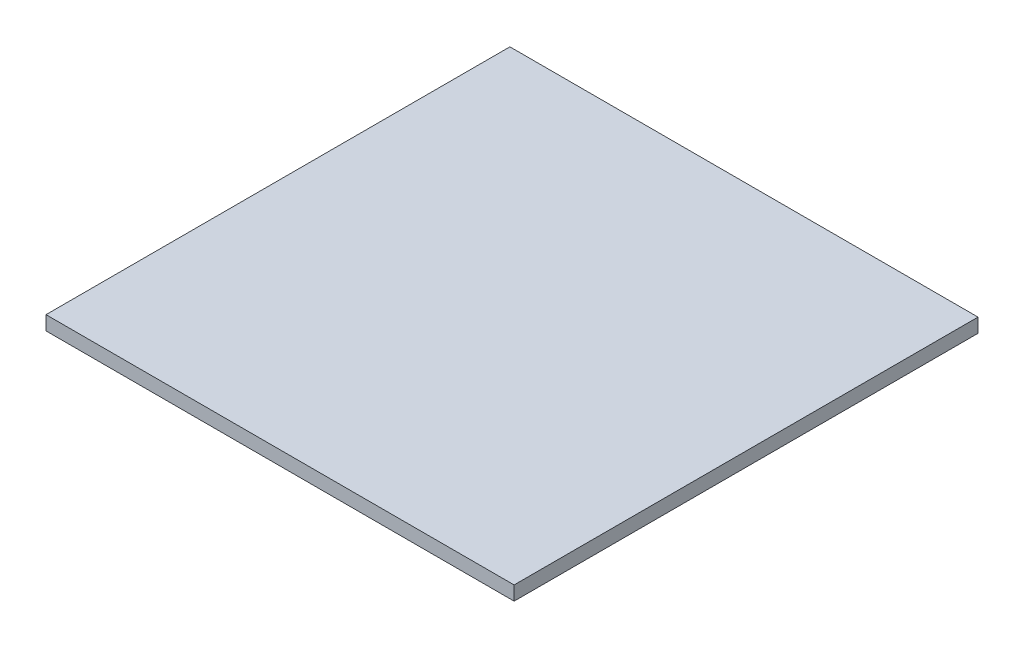
SolidWorks part; units mm, degrees
ref_plane "Front Plane" through (0, 0, 0) normal (0, 0, 1) x (1, 0, 0)
ref_plane "Top Plane" through (0, 0, 0) normal (0, 1, 0) x (1, 0, 0)
ref_plane "Right Plane" through (0, 0, 0) normal (1, 0, 0) x (0, 0, -1)
sketch "Sketch1" plane through (0, 0, 0) normal (0, 1, 0) x (1, 0, 0)
  line L1 (-44.2815, 20.698) -> (55.4185, 20.698)
  line L2 (-44.2815, 20.698) -> (-44.2815, -78.102)
  line L3 (-44.2815, -78.102) -> (55.4185, -78.102)
  line L4 (55.4185, 20.698) -> (55.4185, -78.102)
  dimension "D1" = 99.7
  dimension "D2" = 98.8
extrude "Boss-Extrude1" add sketch "Sketch1" along normal blind 3
equation "\"Fit\"= 1"
equation "\"cover width\"= 98.8"
equation "\"bottom 3 length\"= 99.7"
equation "\"thinner acrylic\" = 3"
equation "\"D1@Sketch1\"=\"bottom 3 length\""
equation "\"D2@Sketch1\"=\"cover width\""
equation "\"D1@Boss-Extrude1\"=\"thinner acrylic\""
